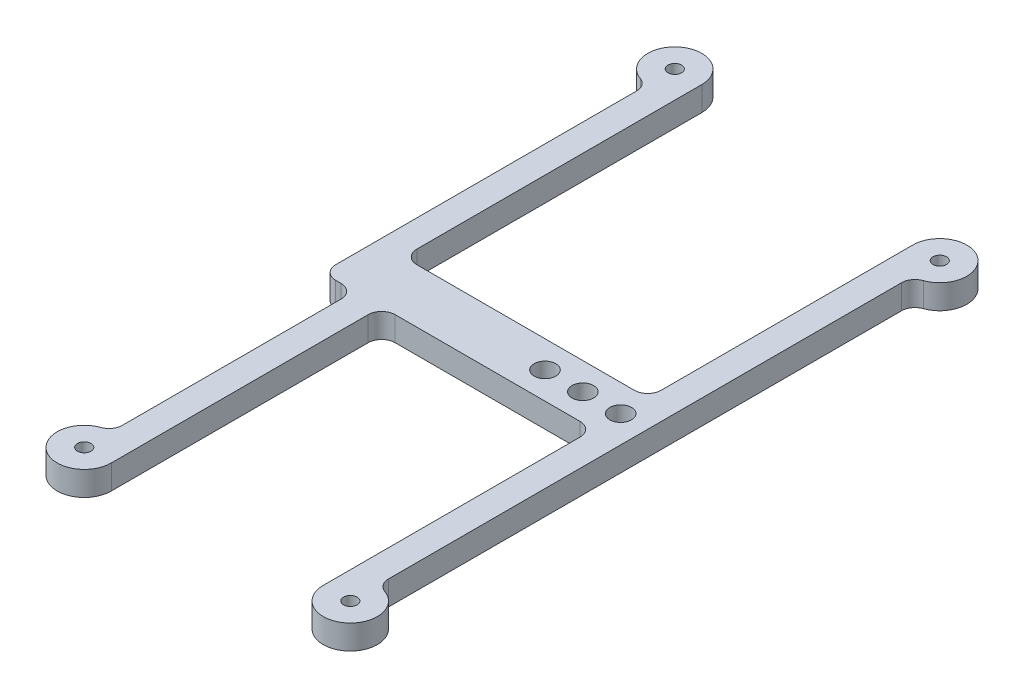
SolidWorks part; units mm, degrees
ref_plane "Front Plane" through (0, 0, 0) normal (0, 0, 1) x (1, 0, 0)
ref_plane "Top Plane" through (0, 0, 0) normal (0, 1, 0) x (1, 0, 0)
ref_plane "Right Plane" through (0, 0, 0) normal (1, 0, 0) x (0, 0, -1)
sketch "Sketch1" plane through (0, 0, 0) normal (0, 1, 0) x (1, 0, 0)
  line L0 (0, 0) -> (49.2, 0) construction
  line L1 (49.2, 0) -> (49.2, 109) construction
  line L2 (49.2, 109) -> (-6, 115.2) construction
  line L3 (-6, 115.2) -> (0, 0) construction
  line L4 (0, 50) -> (-6, 50)
  line L5 (44.2, 50) -> (5, 50)
  line L6 (49.2, 50) -> (49.2, 60)
  line L7 (44.2, 60) -> (-1, 60)
  line L8 (-6, 50) -> (-6, 60)
  line L9 (49.2, 55) -> (-6, 55) construction
  line L10 (0, 5) -> (0, 50)
  line L11 (-1, 115.2) -> (-1, 60)
  line L12 (5, 0) -> (5, 50)
  line L14 (-6, 110.2) -> (-6, 60)
  line L18 (49.2, 104) -> (49.2, 60)
  line L20 (44.2, 109) -> (44.2, 60)
  line L22 (49.2, 5) -> (49.2, 50)
  line L24 (44.2, 0) -> (44.2, 50)
  arc A0 (-1.0312, 114.6419) -> (-6, 110.2) centre (-6, 115.2) ccw
  arc A1 (49.2, 104) -> (44.2, 109) centre (49.2, 109) ccw
  arc A2 (44.2, 0) -> (49.2, 5) centre (49.2, 0) ccw
  arc A3 (0, 5) -> (5, 0) centre (0, 0) ccw
  circle A4 centre (44.2, 55) radius 2
  circle A5 centre (37.2, 55) radius 2
  circle A6 centre (30.2, 55) radius 2
  circle A7 centre (-6, 115.2) radius 1.25
  circle A8 centre (49.2, 109) radius 1.25
  circle A9 centre (0, 0) radius 1.25
  circle A10 centre (49.2, 0) radius 1.25
  dimension "D5" = 10
  dimension "D6" = 10
  dimension "D7" = 10
  dimension "D8" = 10
  dimension "D17" = 4
  dimension "D20" = 4
  dimension "D21" = 4
  dimension "D22" = 2.5
  dimension "D23" = 2.5
  dimension "D24" = 2.5
  dimension "D25" = 2.5
  dimension "D1" = 49.2
  dimension "D2" = 109
  dimension "D3" = 6.2
  dimension "D4" = 6
  dimension "D9" = 10
  dimension "D10" = 50
  dimension "D11" = 10
  dimension "D12" = 5
  dimension "D13" = 5
  dimension "D14" = 5
  dimension "D16" = 5
  dimension "D18" = 7
  dimension "D19" = 7
  dimension "D26" = 5
extrude "Boss-Extrude1" add sketch "Sketch1" along normal blind 4.5
fillet "Fillet5" radius 2.5 10 edges at (0, 2.25, -50) (-6, 2.25, -50) (49.2, 2.25, -104) (-1, 2.25, -60) (49.2, 2.25, -5) (0, 2.25, -5) (44.2, 2.25, -60) (44.2, 2.25, -50) (-6, 2.25, -110.2) (5, 2.25, -50)
